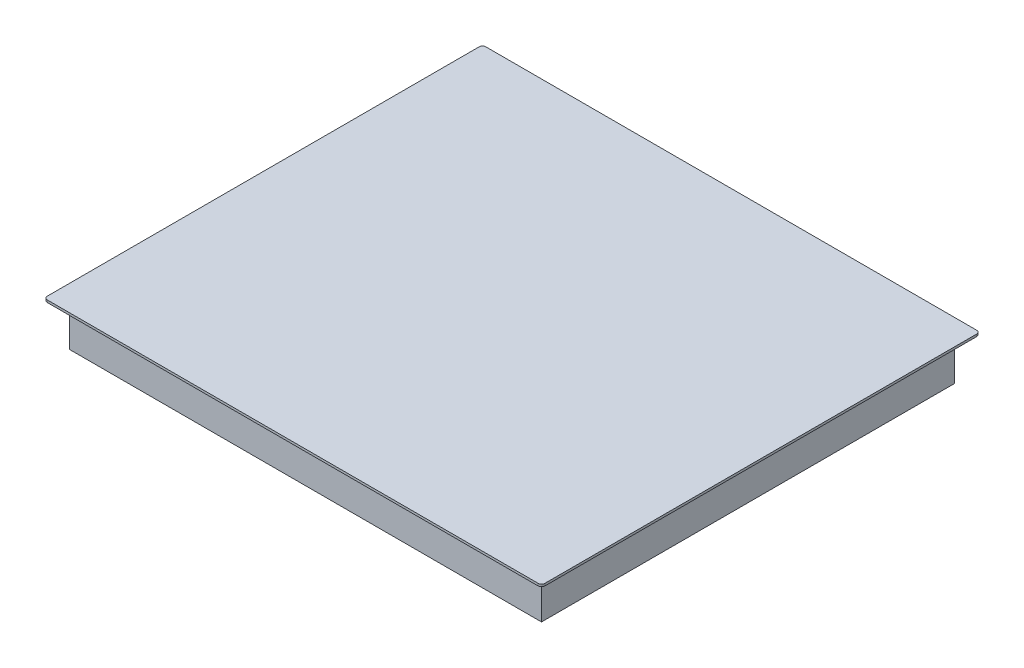
SolidWorks part; units mm, degrees
ref_plane "Front Plane" through (0, 0, 0) normal (0, 0, 1) x (1, 0, 0)
ref_plane "Top Plane" through (0, 0, 0) normal (0, 1, 0) x (1, 0, 0)
ref_plane "Right Plane" through (0, 0, 0) normal (1, 0, 0) x (0, 0, -1)
sketch "Sketch1" plane through (0, 0, 0) normal (0, 1, 0) x (1, 0, 0)
  line L1 (295, -260) -> (-295, -260)
  line L2 (295, -260) -> (295, 260)
  line L3 (295, 260) -> (-295, 260)
  line L4 (-295, -260) -> (-295, 260)
  line L5 (295, -260) -> (-295, 260) construction
  line L6 (295, 260) -> (-295, -260) construction
  point P0 (0, 0)
  dimension "D1" = 520
  dimension "D2" = 590
extrude "Boss-Extrude1" add sketch "Sketch1" along normal blind 2.7
sketch "Sketch2" plane through (0, 0, 0) normal (0, -1, 0) x (1, 0, 0)
  line L1 (280, -245) -> (-280, -245)
  line L2 (280, -245) -> (280, 245)
  line L3 (280, 245) -> (-280, 245)
  line L4 (-280, -245) -> (-280, 245)
  line L5 (280, -245) -> (-280, 245) construction
  line L6 (280, 245) -> (-280, -245) construction
  point P0 (0, 0)
  dimension "D1" = 490
  dimension "D2" = 560
extrude "Boss-Extrude2" add sketch "Sketch2" along normal blind 50
fillet "Fillet1" radius 4 4 edges at (-295, 1.35, -260) (295, 1.35, -260) (295, 1.35, 260) (-295, 1.35, 260)
